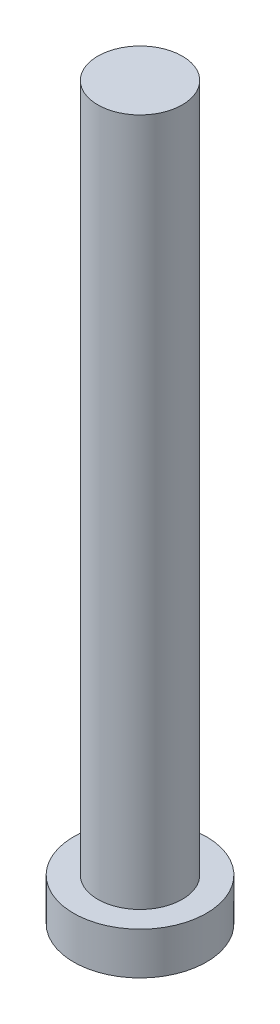
SolidWorks part; units mm, degrees
ref_plane "Plano frontal" through (0, 0, 0) normal (0, 0, 1) x (1, 0, 0)
ref_plane "Plano superior" through (0, 0, 0) normal (0, 1, 0) x (1, 0, 0)
ref_plane "Plano direito" through (0, 0, 0) normal (1, 0, 0) x (0, 0, -1)
sketch "Esboço1" plane through (0, 0, 0) normal (0, 0, 1) x (1, 0, 0)
  line L0 (0, 0) -> (0, 121) construction
  line L1 (0, 121) -> (7, 121)
  line L2 (7, 121) -> (7, 7)
  line L3 (7, 7) -> (11, 7)
  line L4 (11, 7) -> (11, 0)
  line L5 (11, 0) -> (0, 0)
  line L6 (0, 0) -> (0, 121)
  dimension "D1" = 121
  dimension "D2" = 14
  dimension "D3" = 7
  dimension "D4" = 22
revolve "Revolução1" add sketch "Esboço1" angle 360 about L0
